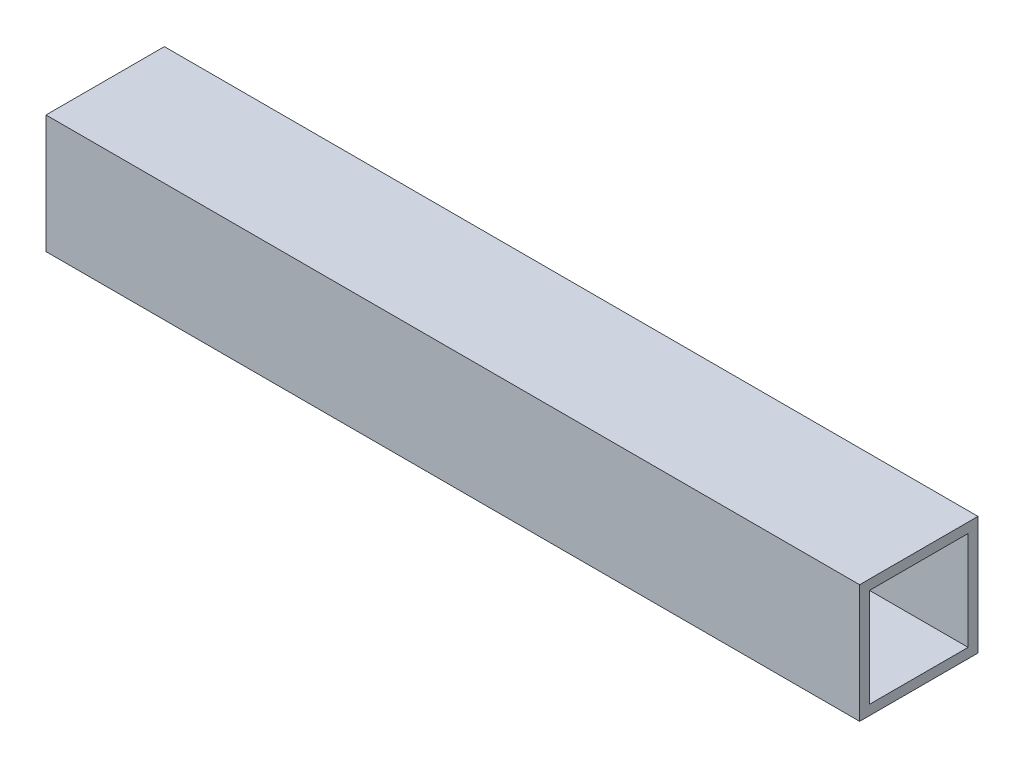
SolidWorks part; units mm, degrees
material "AISI 1020"
ref_plane "Front Plane" through (0, 0, 0) normal (0, 0, 1) x (1, 0, 0)
ref_plane "Top Plane" through (0, 0, 0) normal (0, 1, 0) x (1, 0, 0)
ref_plane "Right Plane" through (0, 0, 0) normal (1, 0, 0) x (0, 0, -1)
sketch "Sketch1" plane through (0, 0, 0) normal (0, 0, 1) x (1, 0, 0)
  line L1 (0, 0) -> (261.9, 0)
  line L2 (0, 0) -> (0, 38.1)
  line L3 (0, 38.1) -> (261.9, 38.1)
  line L4 (261.9, 0) -> (261.9, 38.1)
  dimension "D1" = 261.9
  dimension "D2" = 38.1
extrude "Boss-Extrude1" add sketch "Sketch1" against normal blind 38.1
sketch "Sketch2" plane through (261.9, 0, 0) normal (1, 0, 0) x (0, 0, -1)
  line L1 (38.1, 38.1) -> (0, 38.1) construction
  line L2 (38.1, 38.1) -> (38.1, 0) construction
  line L3 (38.1, 0) -> (0, 0) construction
  line L4 (0, 38.1) -> (0, 0) construction
  line L5 (34.925, 3.175) -> (3.175, 3.175)
  line L6 (34.925, 3.175) -> (34.925, 34.925)
  line L7 (34.925, 34.925) -> (3.175, 34.925)
  line L8 (3.175, 3.175) -> (3.175, 34.925)
  line L9 (34.925, 3.175) -> (3.175, 34.925) construction
  line L10 (34.925, 34.925) -> (3.175, 3.175) construction
  point P6 (0, 19.05)
  point P7 (19.05, 38.1)
  point P8 (19.05, 19.05)
  point P11 (19.05, 19.05)
  dimension "D1" = 3.175
extrude "Cut-Extrude1" cut sketch "Sketch2" against normal through all both and the other way through all
ref_plane "Plane1" through (130.95, 0, 0) normal (1, 0, 0) x (0, 0, -1)
